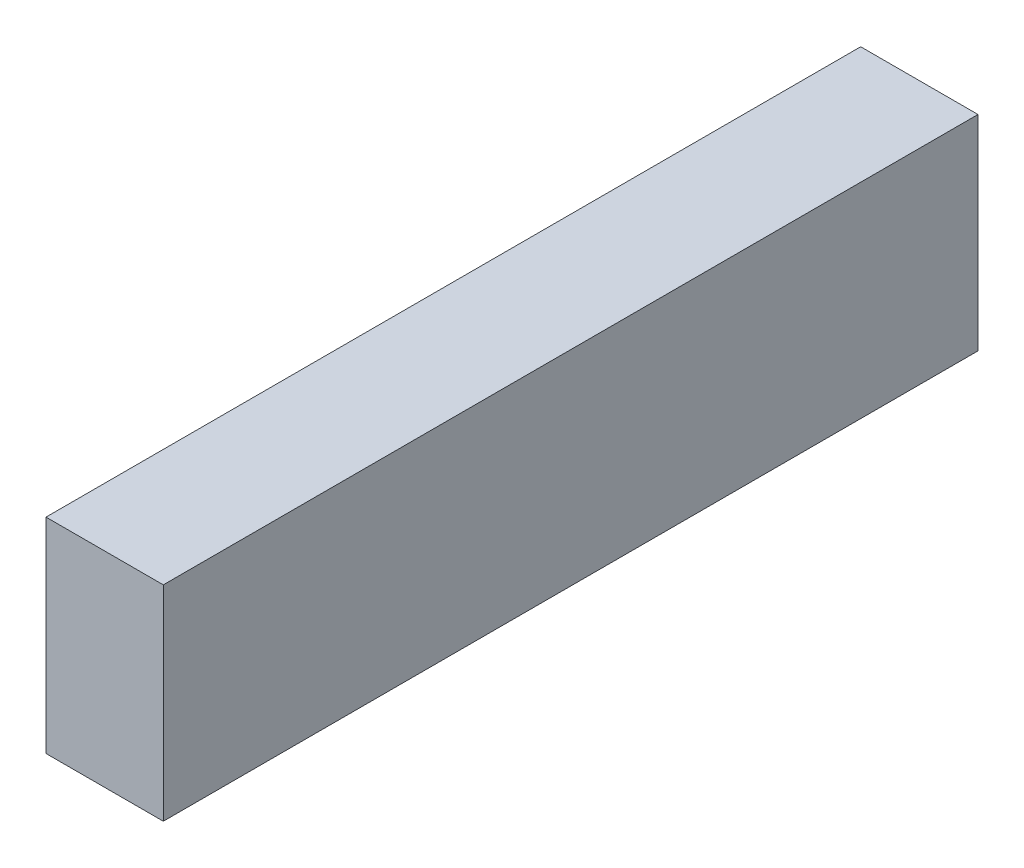
SolidWorks part; units mm, degrees
material "1023 al carbonio, lamiera (SS)"
ref_plane "Piano frontale" through (0, 0, 0) normal (0, 0, 1) x (1, 0, 0)
ref_plane "Piano superiore" through (0, 0, 0) normal (0, 1, 0) x (1, 0, 0)
ref_plane "Piano destro" through (0, 0, 0) normal (1, 0, 0) x (0, 0, -1)
sketch "Schizzo1" plane through (0, 0, 0) normal (0, 0, 1) x (1, 0, 0)
  line L0 (3.6, 12.566) -> (3.6, 0) construction
  line L1 (0, 0) -> (7.2, 0)
  line L2 (0, 0) -> (0, 12.566)
  line L3 (0, 12.566) -> (7.2, 12.566)
  line L4 (7.2, 0) -> (7.2, 12.566)
  dimension "D1" = 12.566
  dimension "D2" = 7.2
extrude "Estrusione-Estrusione1" add sketch "Schizzo1" along normal blind 50
